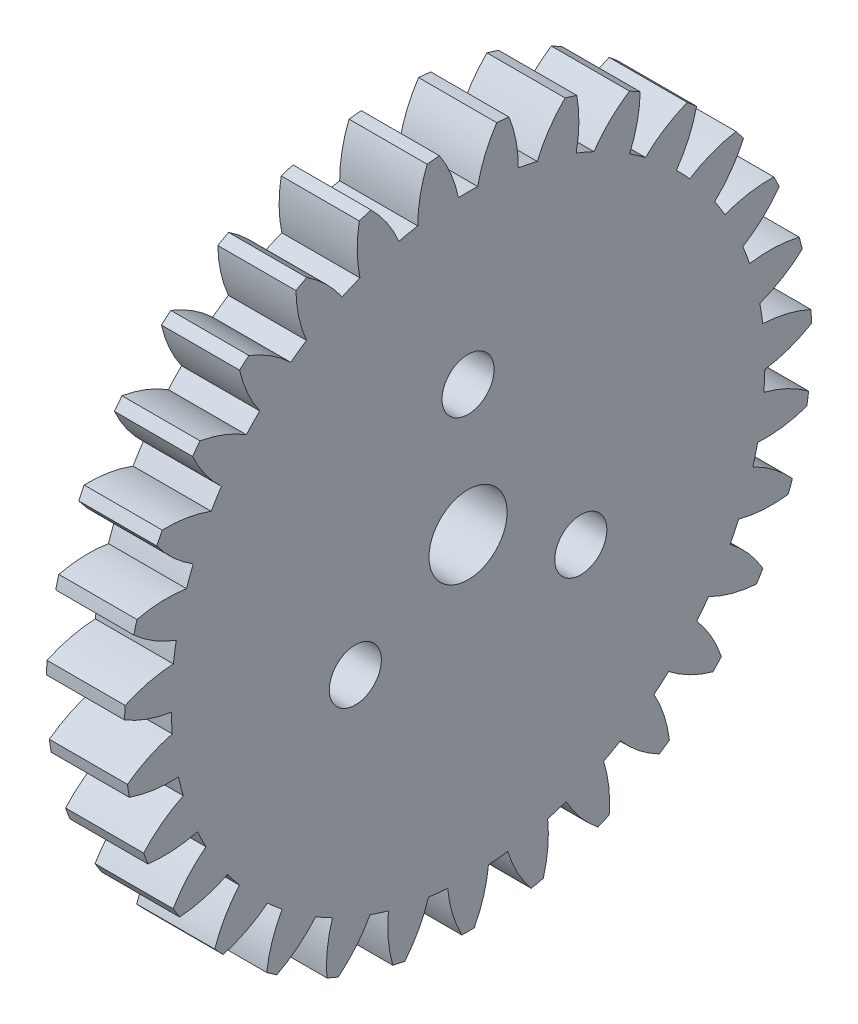
SolidWorks part; units mm, degrees
ref_plane "Plane1" through (0, 0, 0) normal (0, 0, 1) x (1, 0, 0)
ref_plane "Plane2" through (0, 0, 0) normal (0, 1, 0) x (1, 0, 0)
ref_plane "Plane3" through (0, 0, 0) normal (1, 0, 0) x (0, 0, -1)
sketch "HoldingSke" plane through (0, 0, 0) normal (0, 1, 0) x (1, 0, 0)
  line L0 (0, 0) -> (1.0715, -0.6438)
  line L1 (-15, 0) -> (100, 0) construction
  line L2 (0, 0) -> (-2.1039, 2.3779)
  line L3 (0, 0) -> (-11.863, 4.5341)
  line L4 (0, 0) -> (7.4025, 4.4479)
  line L5 (0, 0) -> (-46.8476, -17.4728)
  line L6 (0, 0) -> (-2.4869, -1.6779)
  line L7 (-2.1039, 2.3779) -> (8.6586, 51.2059)
  line L8 (-76.2, 54.61) -> (-75.7, 54.61)
  line L9 (-71.009, 38.7566) -> (-53.1078, 45.2721)
  line L10 (-76.2, 71.12) -> (104.1128, 71.12)
  line L11 (0, 0) -> (-3, 0)
  line L12 (-76.2, 101.6) -> (-76.17, 101.6)
  line L13 (24.9733, 27.94) -> (52.9518, 28.4284)
  line L14 (24.9733, 27.94) -> (24.9743, 27.94)
  line L15 (24.9733, 27.94) -> (100.4006, 29.5858)
  line L16 (-63.627, -0.8) -> (-12.827, -0.8)
  circle A0 centre (0, 0) radius 1.5
  circle A1 centre (0, 0) radius 11.399
  circle A2 centre (0, 0) radius 37.5
  circle A3 centre (0, 0) radius 1.5
  dimension "MHD" = 22.798
  dimension "Hub_dia" = 75
  dimension "Bore" = 3
  dimension "MBD" = 3
  dimension "Num_teeth" = 31
  dimension "Pitch" = 1.25
  dimension "Overall_len" = 50
  dimension "Show_teeth" = 31
  dimension "Thickness" = 3
  dimension "OAL" = 50.0001
  dimension "T_dim" = 0.5
  dimension "Ap" = 20
  dimension "H" = 19.05
  dimension "Pitch_radius" = 180.3128
  dimension "Width" = 3
  dimension "Backlash" = 0.03
  dimension "Addendum_fac" = 1
  dimension "Dedendum_fac" = 1.25
  dimension "Clearance_fac" = 0.25
  dimension "Dedendum_add" = 0.001
  dimension "Module" = 0.8
sketch "BasProSke" plane through (0, 0, 0) normal (0, 1, 0) x (1, 0, 0)
  line L0 (-10, 0) -> (60, 0) construction
  line L1 (0, 0) -> (0, 13.2)
  line L2 (0, 0) -> (3, 0)
  line L3 (3, 0) -> (3, 13.2)
  line L4 (3, 13.2) -> (0, 13.2)
  dimension "Thickness" = 3
  dimension "Diameter" = 26.4
revolve "Base-Revolve" add sketch "BasProSke" angle 360 about L0
sketch "TooCutSke" plane through (0, 0, 0) normal (1, 0, 0) x (0, 0, -1)
  line L1 (0, 0) -> (0, 107) construction
  line L2 (0, 0) -> (-0.6805, 12.3813) construction
  line L3 (0, 0) -> (-2.5063, 24.6462) construction
  line L4 (-0.6805, 12.3813) -> (-1.2531, 12.3231) construction
  arc A0 (0.3706, 11.393) -> (-0.3706, 11.393) centre (0, 0) ccw
  arc A1 (1.116, 13.1782) -> (-1.116, 13.1782) centre (0, 0) ccw
  circle A2 centre (0, 0) radius 12.4 construction
  circle A3 centre (0, 0) radius 11.6522 construction
  arc A4 (-0.3706, 11.393) -> (-1.116, 13.1782) centre (-5.2325, 10.4113) ccw
  arc A5 (1.116, 13.1782) -> (0.3706, 11.393) centre (5.2325, 10.4113) ccw
  dimension "Root_dia" = 22.798
  dimension "Overcut_dia" = 26.4508
  dimension "Pitch_dia" = 24.8
  dimension "Base_dia" = 23.3044
  dimension "Flank_rad" = 4.96
  dimension "Half_ang" = 5.806
  dimension "Half_CT" = 0.5755
extrude "ToothCut" cut sketch "TooCutSke" along normal through all
fillet "Breaks" [suppressed] radius 0.016
fillet "RootFillets" [suppressed] radius 0.201
pattern_circular "TeethCuts" count 31 every 11.613 about axis through (-10, 0, 0) along (1, 0, 0) of "ToothCut", "RootFillets", "Breaks"
sketch "HubNeaOneSke" plane through (0, 0, 0) normal (-1, 0, 0) x (0, 0, 1)
  circle A0 centre (0, 0) radius 11.399
  dimension "Diameter" = 22.798
extrude "HubNearOne" [suppressed] add sketch "HubNeaOneSke" along normal blind 47.0001
sketch "HubNeaBotSke" plane through (0, 0, 0) normal (-1, 0, 0) x (0, 0, 1)
  circle A0 centre (0, 0) radius 11.399
  dimension "Diameter" = 22.798
extrude "HubNearBoth" [suppressed] add sketch "HubNeaBotSke" along normal blind 23.5
ref_plane "FarPln" through (3, 0, 0) normal (1, 0, 0) x (0, 0, -1)
sketch "HubFarSke" plane through (3, 0, 0) normal (1, 0, 0) x (0, 0, -1)
  circle A0 centre (0, 0) radius 11.399
  dimension "Diameter" = 22.798
extrude "HubFar" [suppressed] add sketch "HubFarSke" along normal blind 23.5
sketch "BorSke" plane through (0, 0, 0) normal (1, 0, 0) x (0, 0, -1)
  circle A0 centre (0, 0) radius 1.5
  dimension "Diameter" = 3
extrude "Bore" cut sketch "BorSke" along normal mid plane 100.0001
sketch "KeySke" plane through (0, 0, 0) normal (1, 0, 0) x (0, 0, -1)
  line L0 (-0.6, 0) -> (-0.6, 2)
  line L1 (-0.6, 2) -> (0.6, 2)
  line L2 (0.6, 2) -> (0.6, 0)
  line L3 (0, 0) -> (0, 34) construction
  line L4 (-0.6, 0) -> (0.6, 0)
  dimension "Offset" = 2
  dimension "Width" = 1.2
extrude "Keyway" [suppressed] cut sketch "KeySke" along normal mid plane 100.0001
pattern_circular "Keyway2" [suppressed] count 2 every 90 about axis through (-10, 0, 0) along (1, 0, 0)
sketch "草图1" plane through (3, 0, 0) normal (1, 0, 0) x (0, 0, -1)
  circle A0 centre (0, 0) radius 4.6628
sketch "草图2" plane through (3, 0, 0) normal (1, 0, 0) x (0, 0, -1)
  circle A0 centre (0, 0) radius 5 construction
  circle A1 centre (0, 5) radius 1
  circle A2 centre (4.3301, -2.5) radius 1
  circle A3 centre (-4.3301, -2.5) radius 1
  point P11 (0, 0)
  dimension "D1" = 10
  dimension "D2" = 2
  dimension "D3" = 3
extrude "切除-拉伸1" cut sketch "草图2" against normal blind 5 and the other way blind 12
equation "' \"Module@HoldingSke\" = 6.35"
equation "' \"Num_teeth@HoldingSke\" = 12"
equation "' \"Ap@HoldingSke\" =  20"
equation "' \"Ap@HoldingSke\" = 20"
equation "' \"Width@HoldingSke\" = 0.5 * 25.4"
equation "' \"Hub_dia@HoldingSke\"= 1 * 25.4"
equation "' \"Hub_dia@HoldingSke\" = 1 * 25.4"
equation "' \"Overall_len@HoldingSke\" = 1.0 * 25.4"
equation "' \"Bore@HoldingSke\" = 0.75 * 25.4"
equation "' \"T_dim@HoldingSke\" = 0.1 * 25.4"
equation "' \"Width@KeySke\" = 0.25 * 25.4"
equation "' \"Show_teeth@HoldingSke\" = 13"
equation "' \"Backlash@HoldingSke\" = 0.009 * 25.4"
equation "' \"Addendum_fac@HoldingSke\" = 1.0"
equation "' \"Dedendum_fac@HoldingSke\" = 1.25"
equation "' \"Dedendum_add@HoldingSke\" = 0.00005 * 25.4"
equation "' \"Clearance_fac@HoldingSke\" = 0.25"
equation "\"Pitch@HoldingSke\" = 1 / \"Module@HoldingSke\""
equation "\"Overcut_dia@TooCutSke\" = (\"Num_teeth@HoldingSke\" + 2 * \"Addendum_fac@HoldingSke\") / \"Pitch@HoldingSke\" + 0.002 * 25.4"
equation "\"Pitch_dia@TooCutSke\" = \"Num_teeth@HoldingSke\" / \"Pitch@HoldingSke\""
equation "\"Base_dia@TooCutSke\" = \"Num_teeth@HoldingSke\" / \"Pitch@HoldingSke\" * cos((\"Ap@HoldingSke\"  * 3.14159265 / 180))"
equation "\"Root_dia@TooCutSke\" = (\"Num_teeth@HoldingSke\" + 2) / \"Pitch@HoldingSke\" - 2 * (\"Addendum_fac@HoldingSke\" + \"Dedendum_fac@HoldingSke\") / \"Pitch@HoldingSke\" - \"Dedendum_add@HoldingSke\" * 2"
equation "\"Half_ang@TooCutSke\" = 180 / \"Num_teeth@HoldingSke\""
equation "\"Half_CT@TooCutSke\" = \"Num_teeth@HoldingSke\" / \"Pitch@HoldingSke\" * sin((3.14159265 / 2 / \"Num_teeth@HoldingSke\")) / 2 - 7 * \"Backlash@HoldingSke\" / 4"
equation "\"Flank_rad@TooCutSke\" = \"Num_teeth@HoldingSke\" / \"Pitch@HoldingSke\" / 5"
equation "\"Radius@RootFillets\" = \"Clearance_fac@HoldingSke\" / \"Pitch@HoldingSke\" + \"Dedendum_add@HoldingSke\""
equation "\"Break_rad@Breaks\" = 0.02 / \"Pitch@HoldingSke\""
equation "\"Thickness@HoldingSke\" = \"Width@HoldingSke\""
equation "\"OAL@HoldingSke\" = \"Thickness@HoldingSke\""
equation "\"MHD@HoldingSke\" = (\"Num_teeth@HoldingSke\" + 2) / \"Pitch@HoldingSke\" - 2 * (\"Addendum_fac@HoldingSke\" + \"Dedendum_fac@HoldingSke\")  / \"Pitch@HoldingSke\" - \"Dedendum_add@HoldingSke\" * 2"
equation "\"MBD@HoldingSke\" = (\"Num_teeth@HoldingSke\" + 2) / \"Pitch@HoldingSke\" - 2 * (\"Addendum_fac@HoldingSke\" + \"Dedendum_fac@HoldingSke\")  / \"Pitch@HoldingSke\" - \"Dedendum_add@HoldingSke\" * 2 - 0.002 * 25.4"
equation "\"MHD@HoldingSke\" = ((sgn( \"MHD@HoldingSke\" - \"Hub_dia@HoldingSke\" )-1)*( \"MHD@HoldingSke\" - \"Hub_dia@HoldingSke\" ))/-2+ \"Hub_dia@HoldingSke\""
equation "\"MBD@HoldingSke\" = ((sgn( \"MBD@HoldingSke\" - \"Bore@HoldingSke\" )-1)*( \"MBD@HoldingSke\" - \"Bore@HoldingSke\" ))/-2+ \"Bore@HoldingSke\""
equation "\"OAL@HoldingSke\" = ((sgn( \"OAL@HoldingSke\" - \"Overall_len@HoldingSke\" )+1)*( \"OAL@HoldingSke\" - \"Overall_len@HoldingSke\" ))/2 + \"Overall_len@HoldingSke\" + 0.000002 * 25.4"
equation "\"Num_teeth@TeethCuts\" = int( \"Show_teeth@HoldingSke\" ) + 1"
equation "\"Num_teeth@TeethCuts\" = ((sgn( \"Num_teeth@TeethCuts\" - \"Num_teeth@HoldingSke\" )-1)*( \"Num_teeth@TeethCuts\" - \"Num_teeth@HoldingSke\" ))/-2+ \"Num_teeth@HoldingSke\""
equation "\"Num_teeth@TeethCuts\" = ((sgn( \"Num_teeth@TeethCuts\" - 2.0)+1)*( \"Num_teeth@TeethCuts\" - 2.0))/2 +2.0"
equation "\"Angle@TeethCuts\" = 360.0 / \"Num_teeth@HoldingSke\""
equation "\"Diameter@BasProSke\" = (\"Num_teeth@HoldingSke\" + 2 * \"Addendum_fac@HoldingSke\") / \"Pitch@HoldingSke\""
equation "\"Thickness@BasProSke\"  = \"Thickness@HoldingSke\""
equation "' \"Fillet_rad@BasProSke\" =  \"Thickness@HoldingSke\" * 0.05"
equation "' \"Fillet_rad@BasProSke\" = \"Thickness@HoldingSke\" * 0.05"
equation "\"MHD@HoldingSke\" = ((sgn( \"MHD@HoldingSke\" - \"Root_dia@TooCutSke\" )-1)*( \"MHD@HoldingSke\" - \"Root_dia@TooCutSke\" ))/-2+ \"Root_dia@TooCutSke\""
equation "\"Diameter@HubNeaOneSke\" = \"MHD@HoldingSke\""
equation "\"Length@HubNearOne\" = \"OAL@HoldingSke\" - \"Thickness@BasProSke\""
equation "\"Diameter@HubNeaBotSke\" = \"MHD@HoldingSke\""
equation "\"Length@HubNearBoth\" = ( \"OAL@HoldingSke\" - \"Thickness@BasProSke\" ) / 2.0"
equation "\"Thickness@FarPln\" = \"Thickness@BasProSke\""
equation "\"Diameter@HubFarSke\" = \"MHD@HoldingSke\""
equation "\"Length@HubFar\" = ( \"OAL@HoldingSke\" - \"Thickness@BasProSke\" ) / 2.0"
equation "\"Diameter@BorSke\" = \"MBD@HoldingSke\""
equation "\"D1@Bore\" = \"OAL@HoldingSke\" * 2.0"
equation "\"D1@Keyway\" = \"OAL@HoldingSke\" * 2.0"
equation "\"Offset@KeySke\" = \"T_dim@HoldingSke\" + \"MBD@HoldingSke\" / 2.0"
